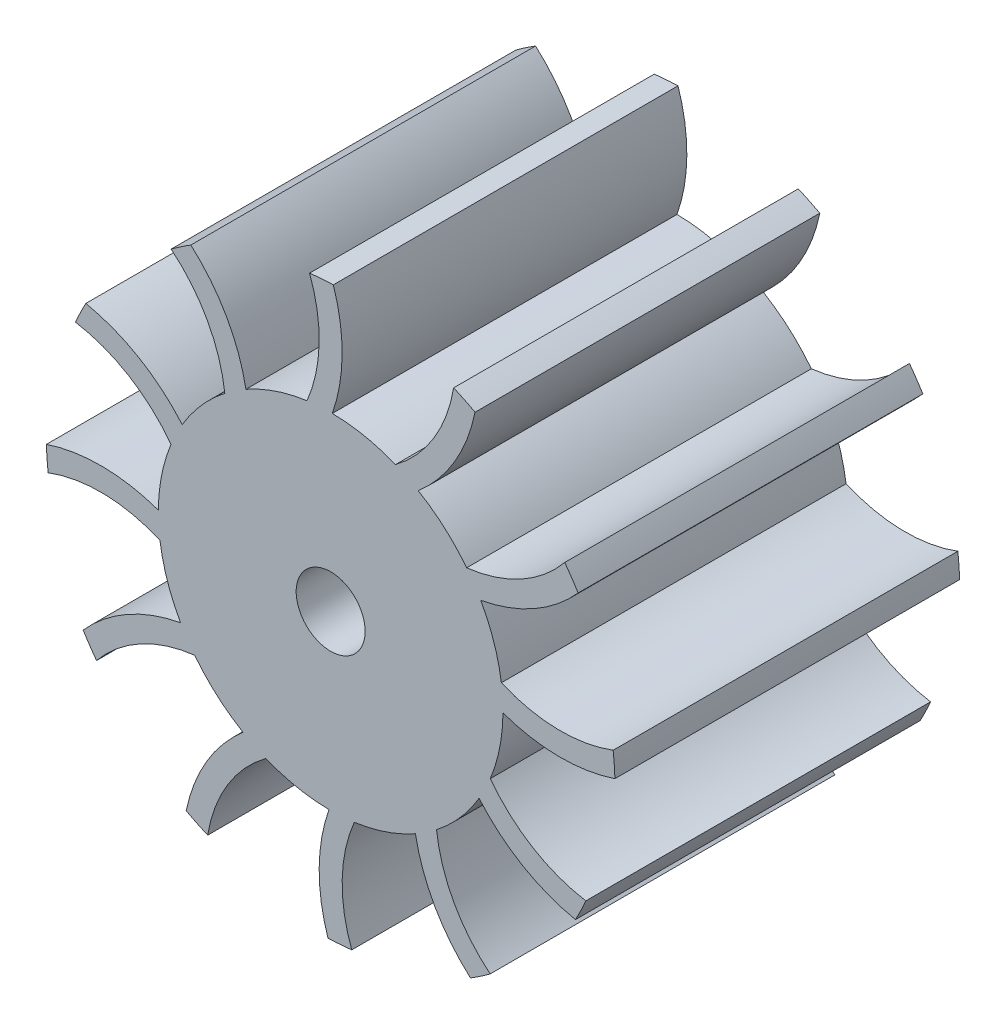
SolidWorks part; units mm, degrees
ref_plane "Front Plane" through (0, 0, 0) normal (0, 0, 1) x (1, 0, 0)
ref_plane "Top Plane" through (0, 0, 0) normal (0, 1, 0) x (1, 0, 0)
ref_plane "Right Plane" through (0, 0, 0) normal (1, 0, 0) x (0, 0, -1)
sketch "Sketch1" plane through (0, 0, 0) normal (0, 0, 1) x (1, 0, 0)
  line L0 (-1, -1000) -> (-1, 49000) construction
  line L1 (-998.1532, -20) -> (49001.8468, -20) construction
  line L2 (3, -13.0718) -> (3, -9.802)
  arc A0 (-0.232, -24.7381) -> (1.8361, -24.587) centre (-1, 0) ccw
  arc A5 (3, -13.0718) -> (1.8361, -24.587) centre (14, -20) ccw
  arc A6 (3, -9.802) -> (-0.232, -24.7381) centre (14, -20) ccw
  point P2 (0, 0)
  dimension "D1" = 15
  dimension "D2" = 2
  dimension "D3" = 20
  dimension "D5" = 24.75
  dimension "D4" = 1
  dimension "D6" = 15
  dimension "D7" = 4
extrude "Boss-Extrude1" add sketch "Sketch1" along normal mid plane 30
sketch "Sketch6" plane through (0, 0, 0) normal (0, 0, 1) x (1, 0, 0)
  circle A0 centre (0, 0) radius 15
  circle A1 centre (0, 0) radius 3
  dimension "D1" = 6
  dimension "D2" = 30
extrude "Boss-Extrude3" add sketch "Sketch6" along normal mid plane 30
pattern_circular "CirPattern3" count 12 over 360 about axis through (0, 0, 0) along (0, 0, 1) of "Boss-Extrude1"
